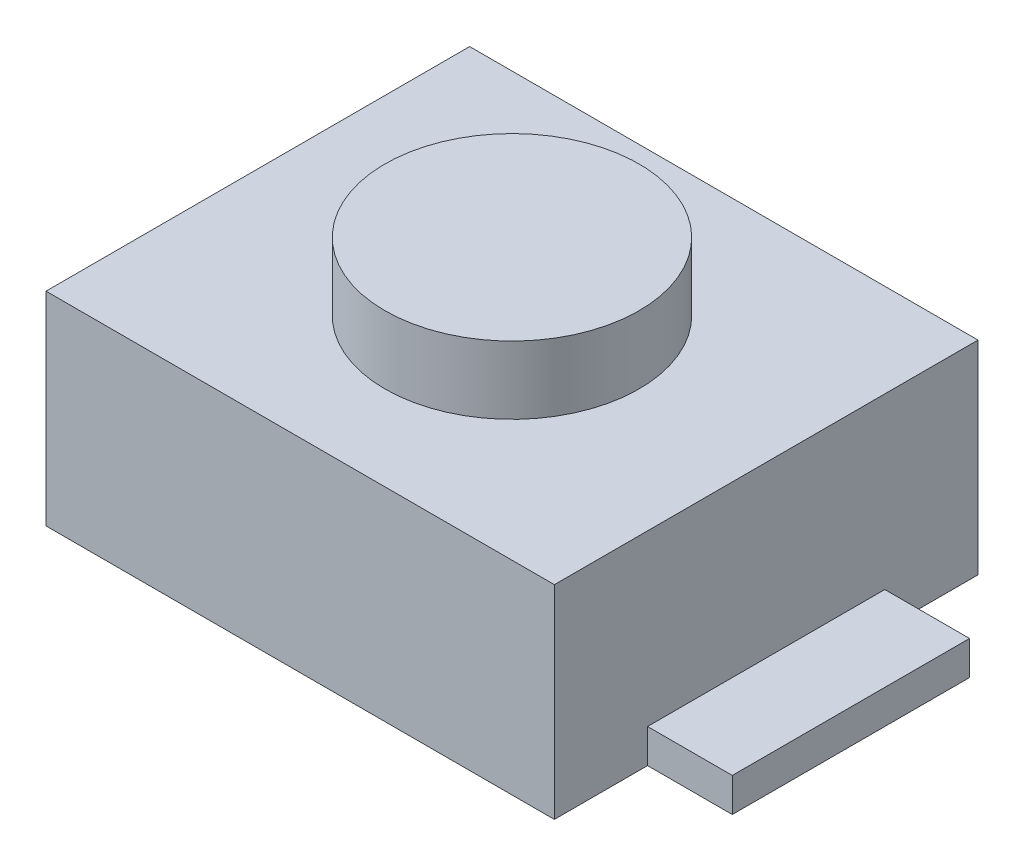
SolidWorks part; units mm, degrees
ref_plane "Front Plane" through (0, 0, 0) normal (0, 0, 1) x (1, 0, 0)
ref_plane "Top Plane" through (0, 0, 0) normal (0, 1, 0) x (1, 0, 0)
ref_plane "Right Plane" through (0, 0, 0) normal (1, 0, 0) x (0, 0, -1)
ref_plane "Plane1" through (0, 0, 0) normal (0, -1, 0) x (1, 0, 0)
sketch "Sketch1" plane through (0, 0, 0) normal (0, -1, 0) x (1, 0, 0)
  line L0 (1.5, -1.25) -> (1.5, 1.25)
  line L1 (1.5, 1.25) -> (-1.5, 1.25)
  line L2 (-1.5, 1.25) -> (-1.5, -1.25)
  line L3 (-1.5, -1.25) -> (1.5, -1.25)
extrude "Boss-Extrude1" add sketch "Sketch1" against normal blind 1.2
sketch "Sketch2" plane through (1.5, 0, 0) normal (1, 0, 0) x (0, 0, -1)
  line L0 (0.7, 0.2) -> (0.7, 0)
  line L1 (0.7, 0) -> (-0.7, 0)
  line L2 (-0.7, 0) -> (-0.7, 0.2)
  line L3 (-0.7, 0.2) -> (0.7, 0.2)
extrude "Boss-Extrude2" add sketch "Sketch2" along normal blind 0.5
sketch "Sketch3" plane through (-1.5, 0, 0) normal (-1, 0, 0) x (0, 0, 1)
  line L0 (0.7, 0) -> (-0.7, 0)
  line L1 (-0.7, 0) -> (-0.7, 0.2)
  line L2 (-0.7, 0.2) -> (0.7, 0.2)
  line L3 (0.7, 0.2) -> (0.7, 0)
extrude "Boss-Extrude3" add sketch "Sketch3" along normal blind 0.5
ref_plane "Plane2" through (0, 0, 0) normal (0, 0, -1) x (-1, 0, 0)
sketch "Sketch4" plane through (0, 0, 0) normal (0, 0, -1) x (-1, 0, 0)
  line L0 (-0.75, 1.2) -> (0, 1.2)
  line L1 (0, 1.2) -> (0, 1.6)
  line L2 (0, 1.6) -> (-0.75, 1.6)
  line L3 (-0.75, 1.6) -> (-0.75, 1.2)
  line L4 (0, 1.2) -> (0, 1.6) construction
revolve "Revolve1" add sketch "Sketch4" angle 360 about L4
